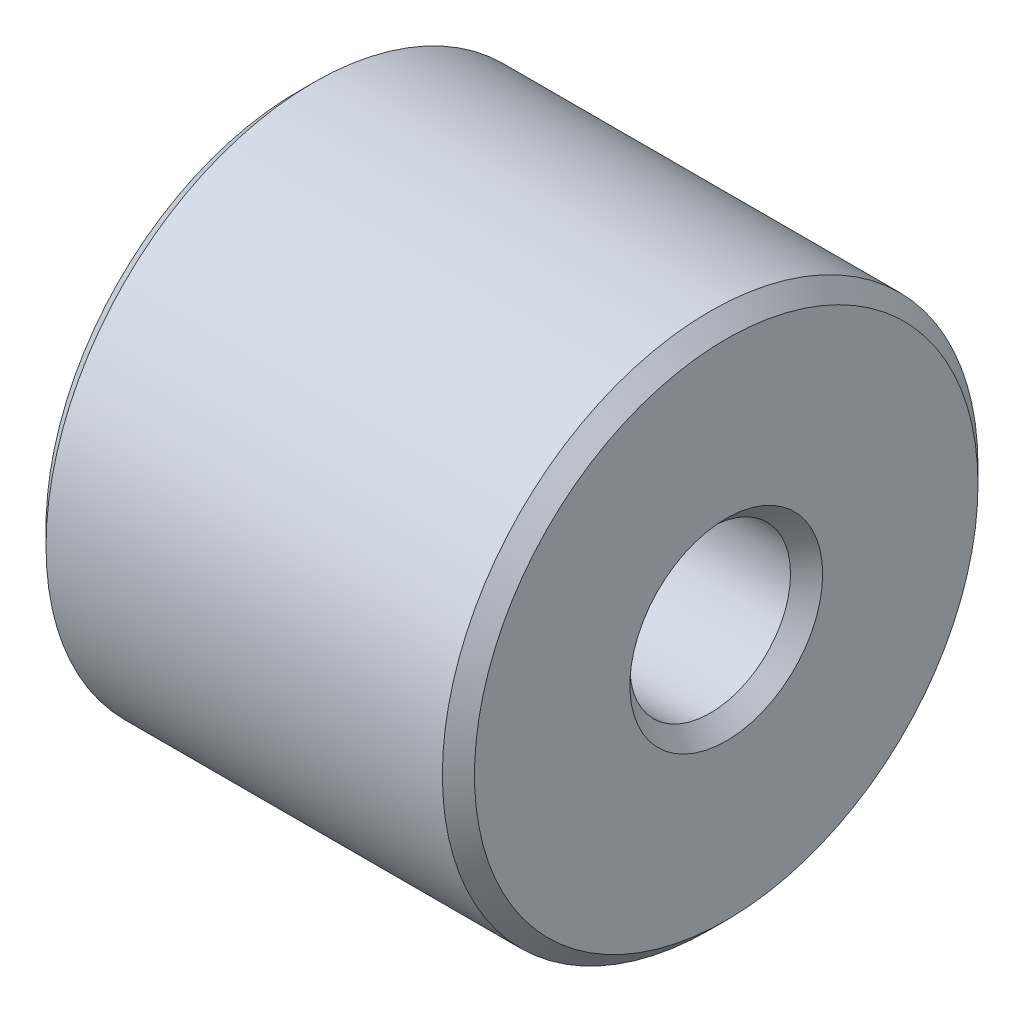
SolidWorks part; units mm, degrees
ref_plane "Front Plane" through (0, 0, 0) normal (0, 0, 1) x (1, 0, 0)
ref_plane "Top Plane" through (0, 0, 0) normal (0, 1, 0) x (1, 0, 0)
ref_plane "Right Plane" through (0, 0, 0) normal (1, 0, 0) x (0, 0, -1)
sketch "Sketch1" plane through (0, 0, 0) normal (1, 0, 0) x (0, 0, -1)
  circle A0 centre (0, 0) radius 2.5
  circle A1 centre (0, 0) radius 0.75
  dimension "D1" = 5
  dimension "D2" = 1.5
extrude "Boss-Extrude1" add sketch "Sketch1" along normal blind 4
chamfer "Chamfer1" distance 0.15 angle 45 4 edges at (0, 0, -0.75) (0, 0, -2.5) (4, 0, -0.75) (4, 0, -2.5)
